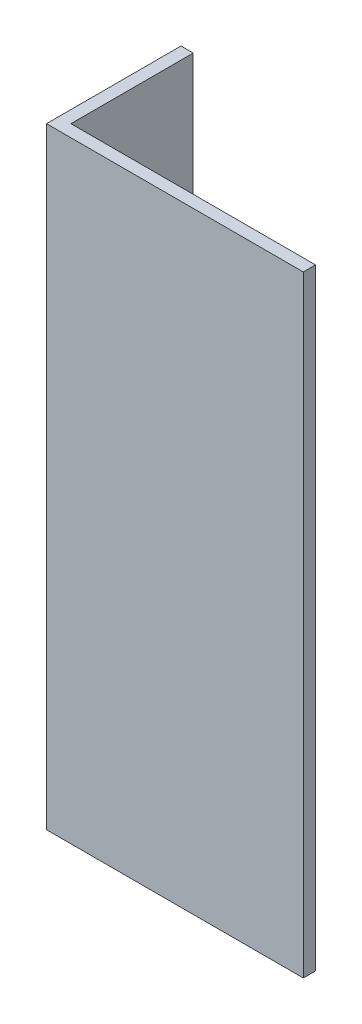
SolidWorks part; units mm, degrees
ref_plane "Plan de face" through (0, 0, 0) normal (0, 0, 1) x (1, 0, 0)
ref_plane "Plan de dessus" through (0, 0, 0) normal (0, 1, 0) x (1, 0, 0)
ref_plane "Plan de droite" through (0, 0, 0) normal (1, 0, 0) x (0, 0, -1)
sketch "Esquisse1" plane through (0, 0, 0) normal (0, 1, 0) x (1, 0, 0)
  line L0 (-11, 9.5) -> (-11, -1.5)
  line L1 (-11, -1.5) -> (10, -1.5)
  line L2 (10, -1.5) -> (10, -0.5)
  line L3 (10, -0.5) -> (-10, -0.5)
  line L4 (-10, -0.5) -> (-10, 9.5)
  line L5 (-10, 9.5) -> (-11, 9.5)
  dimension "D1" = 1
  dimension "D2" = 1
  dimension "D3" = 0.5
  dimension "D4" = 10
  dimension "D5" = 10
  dimension "D6" = 20
extrude "Boss.-Extru.1" add sketch "Esquisse1" along normal blind 50
